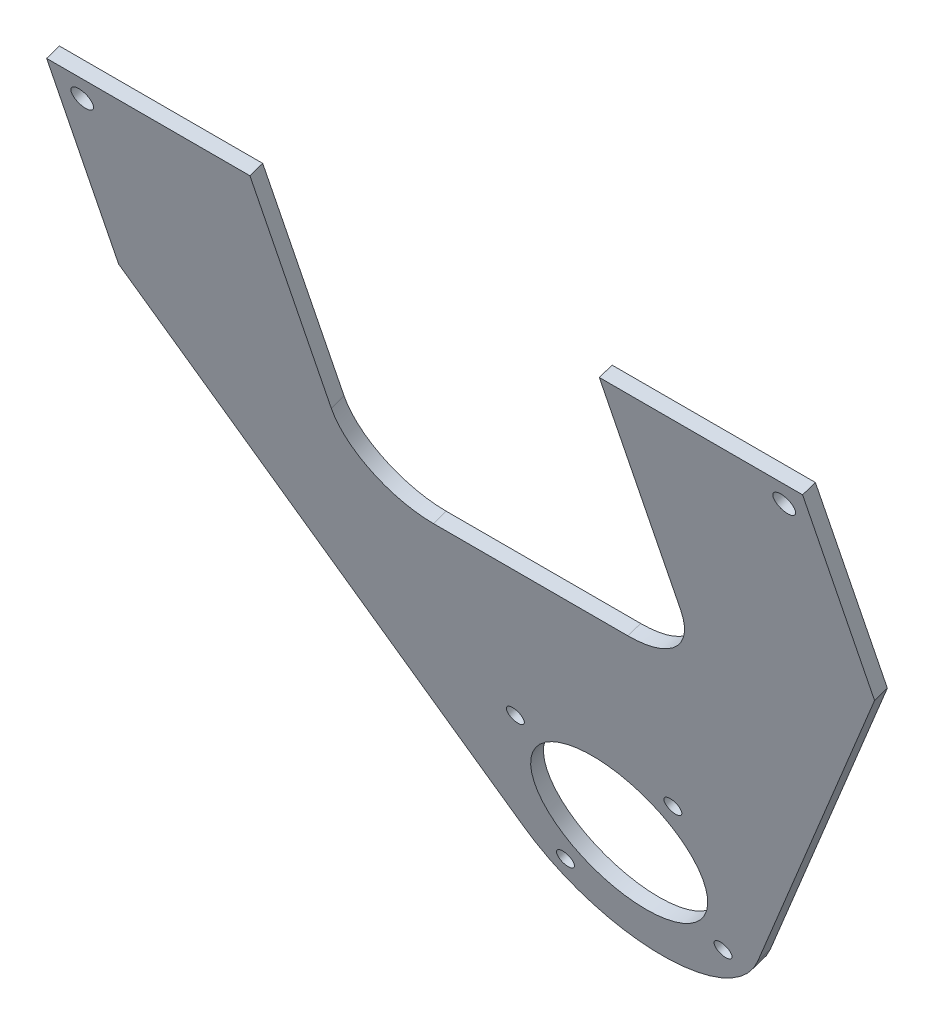
SolidWorks part; units mm, degrees
material "6061-T6 (SS)"
ref_plane "Front" through (0, 0, 0) normal (0, 0, 1) x (1, 0, 0)
ref_plane "Top" through (0, 0, 0) normal (0, 1, 0) x (1, 0, 0)
ref_plane "Right" through (0, 0, 0) normal (1, 0, 0) x (0, 0, -1)
sketch "Sketch1" plane through (0, -335.4888, 998.034) normal (0, -0.3186, 0.9479) x (1, 0, 0)
  line L0 (-88.9, 1035.8684) -> (-88.9, 982.7322)
  line L4 (88.9, 982.7322) -> (88.9, 1035.8684)
  line L5 (88.9, 1035.8684) -> (-88.9, 1035.8684)
  line L7 (27.4963, 876.3779) -> (88.9, 982.7322)
  line L9 (-88.9, 982.7322) -> (-27.4963, 876.3779)
  line L10 (-27.4963, 876.3779) -> (-58.7894, 930.5791) construction
  line L11 (58.7894, 930.5791) -> (27.4963, 876.3779) construction
  arc A7 (-27.4963, 876.3779) -> (27.4963, 876.3779) centre (0, 892.2529) ccw construction
  arc A8 (-27.4963, 876.3779) -> (27.4963, 876.3779) centre (0, 892.2529) ccw
  circle A13 centre (0, 892.2529) radius 19.8437
  dimension "D1" = 39.6875
extrude "Boss-Extrude1" add sketch "Sketch1" along normal blind 3.175
hole_wizard "1/4-20 Tapped Hole1" positions "Sketch2" profile "Sketch3" tap size "1/4-20" standard "ANSI Inch" end condition through all
sketch "Sketch2" plane through (0, -336.5004, 1001.0435) normal (0, -0.3186, 0.9479) x (1, 0, 0)
  circle A2 centre (82.55, 1029.5184) radius 2.5527 construction
  circle A3 centre (-82.55, 1029.5184) radius 2.5527 construction
  point P0 (82.55, 1029.5184)
  point P2 (-82.55, 1029.5184)
sketch "Sketch3" plane through (82.55, 639.3588, 1329.0783) normal (1, 0, 0) x (0, -0.9479, -0.3186)
  line L0 (0, 0) -> (0, 56.1393)
  line L1 (0, 56.1393) -> (2.5527, 56.1393)
  line L2 (2.5527, 56.1393) -> (2.5527, 0)
  line L5 (2.5527, 0) -> (0, 0)
  line L11 (0, -6.35) -> (0, 107.95) construction
  dimension "Thru Tap Drill Dia." = 5.1054
  dimension "Thru Tap Drill Depth" = 56.1393
cosmetic thread "Hole Thread1" parameters "D2"=6.35
cosmetic thread "Hole Thread2" parameters "D2"=6.35
hole_wizard "#10-32 Tapped Hole1" positions "Sketch4" profile "Sketch5" tap size "#10-32" standard "ANSI Inch" end condition through all
sketch "Sketch4" plane through (0, -336.5004, 1001.0435) normal (0, -0.3186, 0.9479) x (1, 0, 0)
  point P0 (18.5218, 873.7311)
  point P2 (-18.5218, 873.7311)
  point P4 (-18.5218, 910.7747)
  point P6 (18.5218, 910.7747)
sketch "Sketch5" plane through (18.5218, 491.6913, 1279.4399) normal (1, 0, 0) x (0, -0.9479, -0.3186)
  line L0 (0, 0) -> (0, 56.1393)
  line L1 (0, 56.1393) -> (2.0193, 56.1393)
  line L2 (2.0193, 56.1393) -> (2.0193, 0)
  line L5 (2.0193, 0) -> (0, 0)
  line L11 (0, -6.35) -> (0, 107.95) construction
  dimension "Thru Tap Drill Dia." = 4.0386
  dimension "Thru Tap Drill Depth" = 56.1393
cosmetic thread "Hole Thread3" parameters "D2"=4.826
cosmetic thread "Hole Thread4" parameters "D2"=4.826
cosmetic thread "Hole Thread5" parameters "D2"=4.826
cosmetic thread "Hole Thread6" parameters "D2"=4.826
sketch "Sketch6" plane through (0, -335.4888, 998.034) normal (0, 0.3186, -0.9479) x (-1, 0, 0)
  line L23 (-12.7, 980.2368) -> (-12.7, 970.2733)
  line L25 (12.7, 970.2733) -> (12.7, 980.2368)
  line L27 (19.05, 986.5868) -> (22.86, 986.5868)
  line L44 (-41.0905, 1046.4733) -> (-41.0905, 1004.8173)
  line L45 (-22.86, 986.5868) -> (-19.05, 986.5868)
  line L46 (41.0905, 1004.8173) -> (41.0905, 1046.4733)
  line L47 (41.0905, 1046.4733) -> (-41.0905, 1046.4733)
  line L48 (-41.0905, 975.8037) -> (-41.0905, 1046.4733)
  line L49 (22.86, 957.5733) -> (-22.86, 957.5733)
  line L50 (41.0905, 1046.4733) -> (41.0905, 975.8037)
  line L51 (41.0905, 1046.4733) -> (-41.0905, 1046.4733)
  arc A0 (-41.0905, 975.8037) -> (-22.86, 957.5733) centre (-22.86, 975.8037) ccw
  arc A1 (-12.7, 970.2733) -> (12.7, 970.2733) centre (0, 970.2733) ccw construction
  arc A2 (41.0905, 975.8037) -> (22.86, 957.5733) centre (22.86, 975.8037) cw
  arc A5 (-12.7, 980.2368) -> (-19.05, 986.5868) centre (-19.05, 980.2368) ccw
  arc A7 (-12.7, 970.2733) -> (12.7, 970.2733) centre (0, 970.2733) ccw
  arc A9 (19.05, 986.5868) -> (12.7, 980.2368) centre (19.05, 980.2368) ccw
  arc A18 (-41.0905, 1004.8173) -> (-22.86, 986.5868) centre (-22.86, 1004.8173) ccw
  arc A20 (22.86, 986.5868) -> (41.0905, 1004.8173) centre (22.86, 1004.8173) ccw
  dimension "D1" = 0
extrude "Cut-Extrude1" cut sketch "Sketch6" against normal through all
